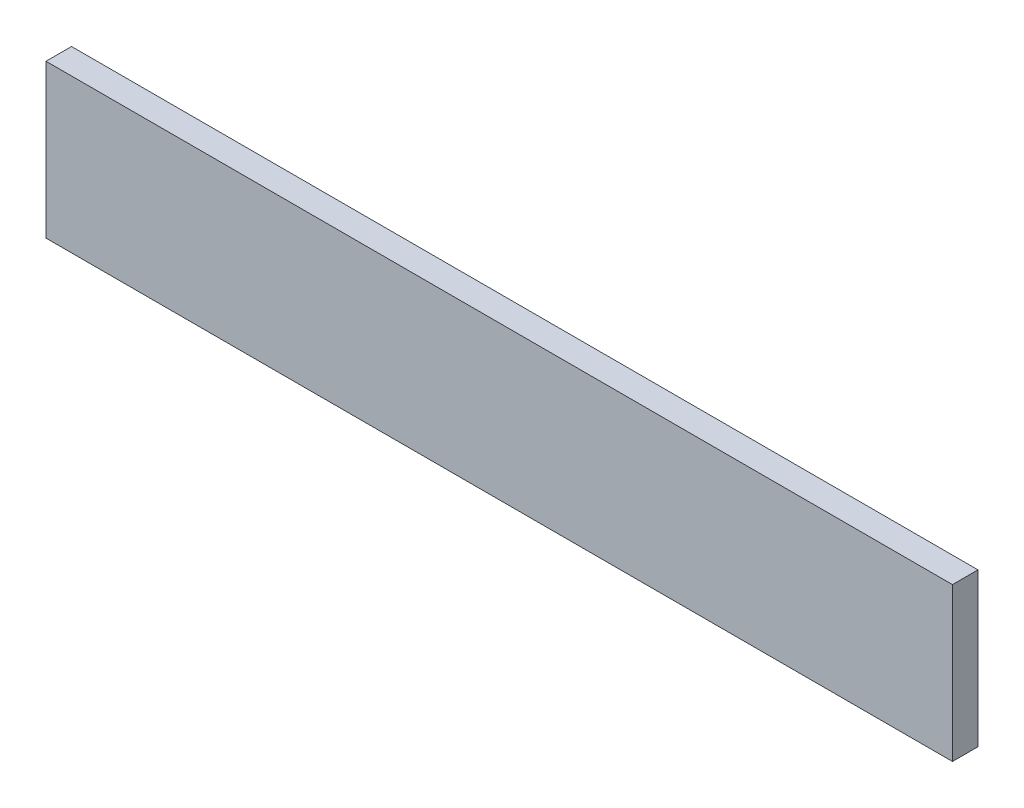
SolidWorks part; units mm, degrees
ref_plane "Front Plane" through (0, 0, 0) normal (0, 0, 1) x (1, 0, 0)
ref_plane "Top Plane" through (0, 0, 0) normal (0, 1, 0) x (1, 0, 0)
ref_plane "Right Plane" through (0, 0, 0) normal (1, 0, 0) x (0, 0, -1)
sketch "Sketch1" plane through (0, 0, 0) normal (0, 0, 1) x (1, 0, 0)
  line L1 (0, 0) -> (710, 0)
  line L2 (0, 0) -> (0, 120)
  line L3 (0, 120) -> (710, 120)
  line L4 (710, 0) -> (710, 120)
  dimension "D1" = 710
  dimension "D2" = 120
extrude "Boss-Extrude1" add sketch "Sketch1" along normal blind 20
